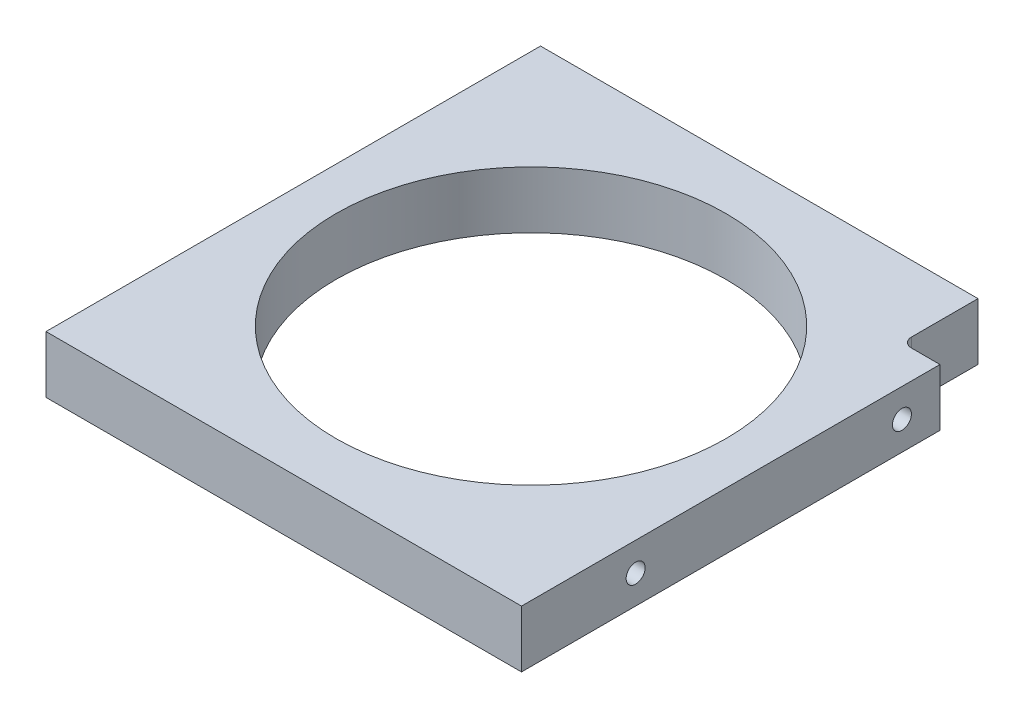
SolidWorks part; units mm, degrees
material "ABS"
ref_plane "Front Plane" through (0, 0, 0) normal (0, 0, 1) x (1, 0, 0)
ref_plane "Top Plane" through (0, 0, 0) normal (0, 1, 0) x (1, 0, 0)
ref_plane "Right Plane" through (0, 0, 0) normal (1, 0, 0) x (0, 0, -1)
sketch "Sketch1" plane through (0, 0, 0) normal (0, 1, 0) x (1, 0, 0)
  line L1 (39.6875, -41.275) -> (-39.6875, -41.275)
  line L2 (39.6875, -41.275) -> (39.6875, 41.275)
  line L3 (39.6875, 41.275) -> (-39.6875, 41.275)
  line L4 (-39.6875, -41.275) -> (-39.6875, 41.275)
  line L5 (39.6875, -41.275) -> (-39.6875, 41.275) construction
  line L6 (39.6875, 41.275) -> (-39.6875, -41.275) construction
  circle A0 centre (0, 0) radius 32.5437
  point P0 (0, 0)
  dimension "D2" = 65.0875
  dimension "D1" = 79.375
  dimension "D3" = 82.55
extrude "Boss-Extrude1" add sketch "Sketch1" along normal mid plane 9.525
sketch "Sketch2" plane through (-39.6875, 0, 0) normal (-1, 0, 0) x (0, 0, 1)
  line L0 (-41.275, 0) -> (-22.225, 0) construction
  line L1 (-41.275, 4.7625) -> (-41.275, -4.7625) construction
  line L4 (41.275, 0) -> (22.225, 0) construction
  line L5 (41.275, 4.7625) -> (41.275, -4.7625) construction
  circle A0 centre (-22.225, 0) radius 1.5875
  circle A1 centre (22.225, 0) radius 1.5875
  dimension "D1" = 3.175
  dimension "D2" = 19.05
extrude "Cut-Extrude1" cut sketch "Sketch2" against normal blind 12.7
mirror "Mirror1" about plane through (0, 0, 0) normal (1, 0, 0) of "Cut-Extrude1"
sketch "Sketch3" plane through (34.925, 4.7625, 0) normal (0, -1, 0) x (0, 0, -1)
  line L1 (41.275, 4.7625) -> (28.575, 4.7625)
  line L2 (41.275, 4.7625) -> (41.275, -1.5875)
  line L3 (41.275, -1.5875) -> (28.575, -1.5875)
  line L4 (28.575, 4.7625) -> (28.575, -1.5875)
  dimension "D1" = 6.35
  dimension "D2" = 12.7
extrude "Cut-Extrude2" cut sketch "Sketch3" along normal through all
fillet "Fillet1" radius 1.5875 1 edges at (33.3375, 0, -28.575)
